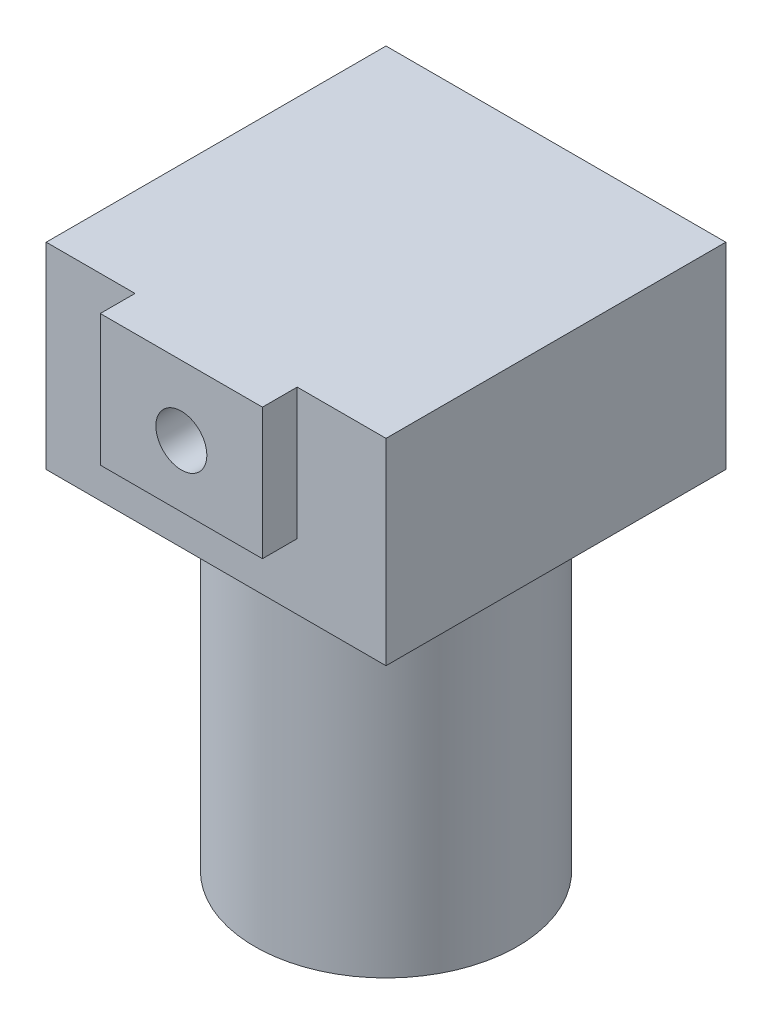
SolidWorks part; units mm, degrees
ref_plane "Front Plane" through (0, 0, 0) normal (0, 0, 1) x (1, 0, 0)
ref_plane "Top Plane" through (0, 0, 0) normal (0, 1, 0) x (1, 0, 0)
ref_plane "Right Plane" through (0, 0, 0) normal (1, 0, 0) x (0, 0, -1)
sketch "Sketch1" plane through (0, 0, 0) normal (0, 1, 0) x (1, 0, 0)
  line L1 (0, 0) -> (44, 0)
  line L2 (0, 0) -> (0, 48.5)
  line L3 (0, 48.5) -> (44, 48.5)
  line L4 (44, 0) -> (44, 48.5)
  dimension "D1" = 44
  dimension "D2" = 48.5
extrude "Boss-Extrude1" add sketch "Sketch1" along normal blind 25.5
sketch "Sketch2" plane through (0, 0, 0) normal (0, 0, 1) x (1, 0, 0)
  line L5 (0, 25.5) -> (44, 25.5) construction
  line L6 (11.5, 25.5) -> (32.5, 25.5)
  line L7 (11.5, 25.5) -> (11.5, 8.5)
  line L8 (11.5, 8.5) -> (32.5, 8.5)
  line L9 (32.5, 25.5) -> (32.5, 8.5)
  line L10 (11.5, 25.5) -> (0, 25.5)
  line L11 (0, 25.5) -> (0, 0)
  line L12 (0, 0) -> (44, 0)
  line L13 (44, 0) -> (44, 25.5)
  line L14 (44, 25.5) -> (32.5, 25.5)
  point P6 (22, 25.5)
  point P7 (22, 25.5)
  line M5 (0, 0) -> (44, 0)
  line M6 (44, 0) -> (44, 25.5)
  line M7 (44, 25.5) -> (0, 25.5)
  line M8 (0, 25.5) -> (0, 0)
  dimension "D1" = 21
  dimension "D2" = 17
extrude "Cut-Extrude1" cut sketch "Sketch2" against normal blind 4.5 contours L9 L8 L7 M7 M8 M5 M6
sketch "Sketch3" plane through (0, 0, 0) normal (0, 0, 1) x (1, 0, 0)
  line L0 (11.5, 25.5) -> (32.5, 25.5) construction
  circle A0 centre (22, 16.5) radius 3.3
  point P5 (22, 25.5)
  dimension "D2" = 6.6
  dimension "D1" = 9
extrude "Cut-Extrude2" cut sketch "Sketch3" against normal blind 7
sketch "Sketch4" plane through (0, 0, 0) normal (0, -1, 0) x (1, 0, 0)
  line L0 (0, -48.5) -> (0, -4.5) construction
  line L1 (44, -48.5) -> (0, -48.5) construction
  circle A0 centre (22, -26.5) radius 17
  point P5 (0, -26.5)
  point P9 (22, -48.5)
  dimension "D1" = 34
extrude "Boss-Extrude2" add sketch "Sketch4" along normal blind 45 contours A0
